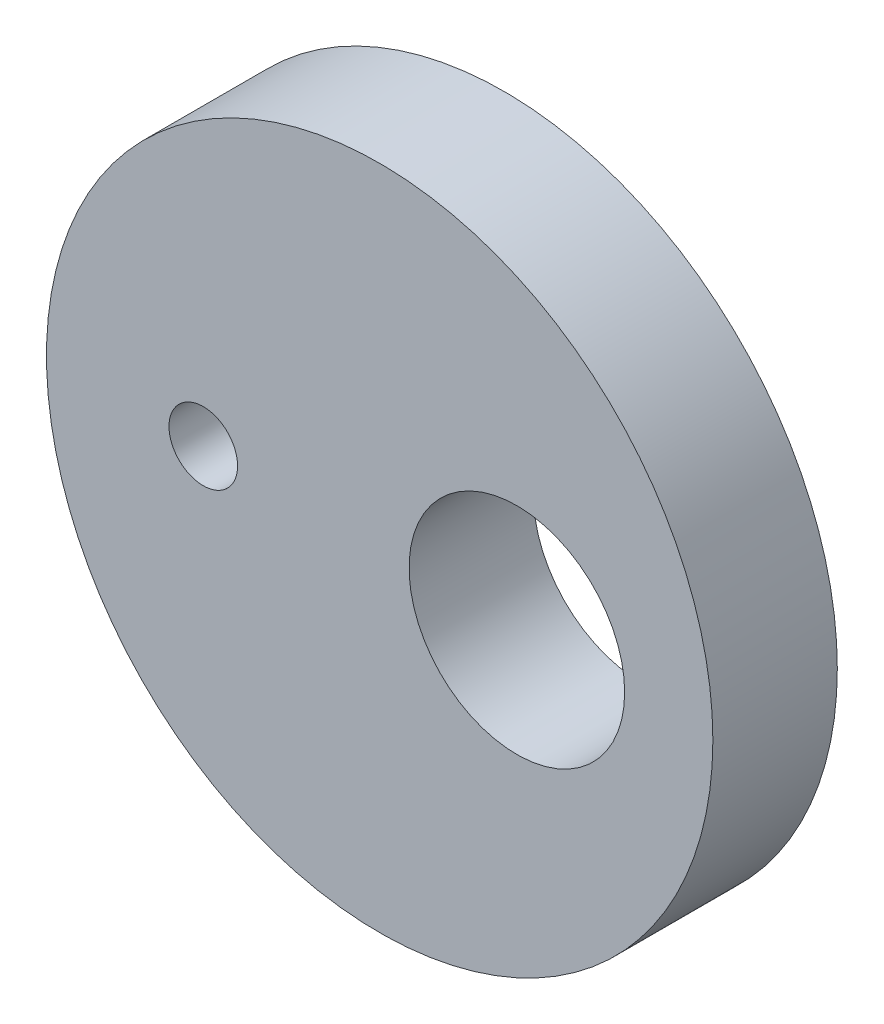
SolidWorks part; units mm, degrees
material "Acrylic (Medium-high impact)"
ref_plane "Front Plane" through (0, 0, 0) normal (0, 0, 1) x (1, 0, 0)
ref_plane "Top Plane" through (0, 0, 0) normal (0, 1, 0) x (1, 0, 0)
ref_plane "Right Plane" through (0, 0, 0) normal (1, 0, 0) x (0, 0, -1)
sketch "Sketch1" plane through (0, 0, 0) normal (0, 0, 1) x (1, 0, 0)
  circle A0 centre (0, 0) radius 17
  circle A1 centre (-9, 0) radius 1.75
  circle A2 centre (7, -0.1255) radius 5.5
  dimension "D1" = 34
  dimension "D3" = 11
  dimension "D4" = 3.5
  dimension "D2" = 9
  dimension "D5" = 7
extrude "Boss-Extrude1" add sketch "Sketch1" along normal blind 6.35 contours A0 A1
